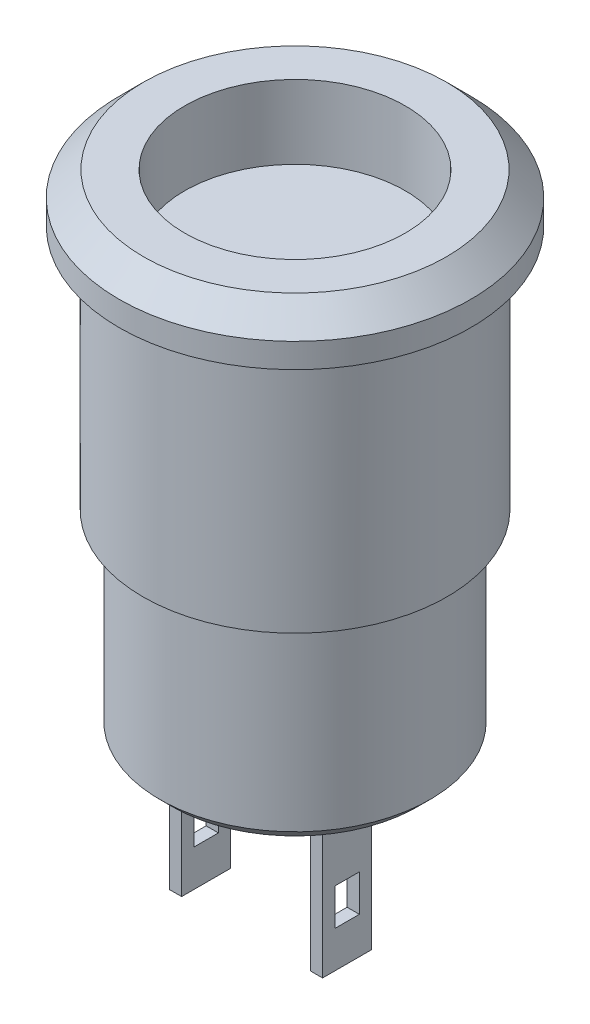
SolidWorks part; units mm, degrees
ref_plane "Front Plane" through (0, 0, 0) normal (0, 0, 1) x (1, 0, 0)
ref_plane "Top Plane" through (0, 0, 0) normal (0, 1, 0) x (1, 0, 0)
ref_plane "Right Plane" through (0, 0, 0) normal (1, 0, 0) x (0, 0, -1)
sketch "Sketch1" plane through (0, 0, 0) normal (0, 1, 0) x (1, 0, 0)
  circle A0 centre (0, 0) radius 7.175
extrude "Boss-Extrude1" add sketch "Sketch1" along normal blind 2
sketch "Sketch2" plane through (0, 0, 0) normal (0, -1, 0) x (1, 0, 0)
  circle A0 centre (0, 0) radius 6.2
extrude "Boss-Extrude2" add sketch "Sketch2" along normal blind 10
sketch "Sketch3" plane through (0, -10, 0) normal (0, -1, 0) x (1, 0, 0)
  circle A0 centre (0, 0) radius 5.515
extrude "Boss-Extrude3" add sketch "Sketch3" along normal blind 8
chamfer "Chamfer2" distance 1 angle 45 1 edges at (0, 2, 7.175)
chamfer "Chamfer3" distance 0.5 angle 45 1 edges at (0, -18, -5.515)
sketch "Sketch4" plane through (0, -18, 0) normal (0, -1, 0) x (1, 0, 0)
  line L0 (0, 0) -> (2.625, 0) construction
  line L1 (2.625, 0) -> (-2.625, 0) construction
  line L3 (2.625, 0) -> (3.125, 0)
  line L4 (2.625, 0) -> (2.625, 2)
  line L5 (2.625, 2) -> (3.125, 2)
  line L6 (3.125, 0) -> (3.125, 2)
  line L7 (-2.625, 0) -> (-3.125, 0)
  line L8 (-2.625, 0) -> (-2.625, 2)
  line L9 (-2.625, 2) -> (-3.125, 2)
  line L10 (-3.125, 0) -> (-3.125, 2)
extrude "Boss-Extrude4" add sketch "Sketch4" along normal blind 6
sketch "Sketch5" plane through (-3.125, 0, 0) normal (-1, 0, 0) x (0, 0, 1)
  line L0 (2, -24) -> (0, -24) construction
  line L1 (0.5, -21) -> (1.5, -21)
  line L2 (0.5, -21) -> (0.5, -22.5)
  line L3 (0.5, -22.5) -> (1.5, -22.5)
  line L4 (1.5, -21) -> (1.5, -22.5)
  line L5 (0.5, -21) -> (1.5, -22.5) construction
  line L6 (0.5, -22.5) -> (1.5, -21) construction
  line L7 (2, -24) -> (2, -18) construction
  line L8 (0, -24) -> (0, -18) construction
  point P0 (1, -21.75)
  dimension "D1" = 1.5
  dimension "D2" = 0.5
  dimension "D3" = 0.5
  dimension "D4" = 1.5
extrude "Cut-Extrude1" cut sketch "Sketch5" against normal through all
sketch "Sketch6" plane through (0, 2, 0) normal (0, 1, 0) x (1, 0, 0)
  circle A0 centre (0, 0) radius 4.5
sketch "Sketch7" plane through (0, -18, 0) normal (0, -1, 0) x (-1, 0, 0)
  text T0 "  3A125VAC\r\n1.5A250VAC" font "Century Gothic" height 0.7
extrude "Boss-Extrude6" add sketch "Sketch7" along normal blind 0.1
extrude "Cut-Extrude2" cut sketch "Sketch6" against normal blind 3
